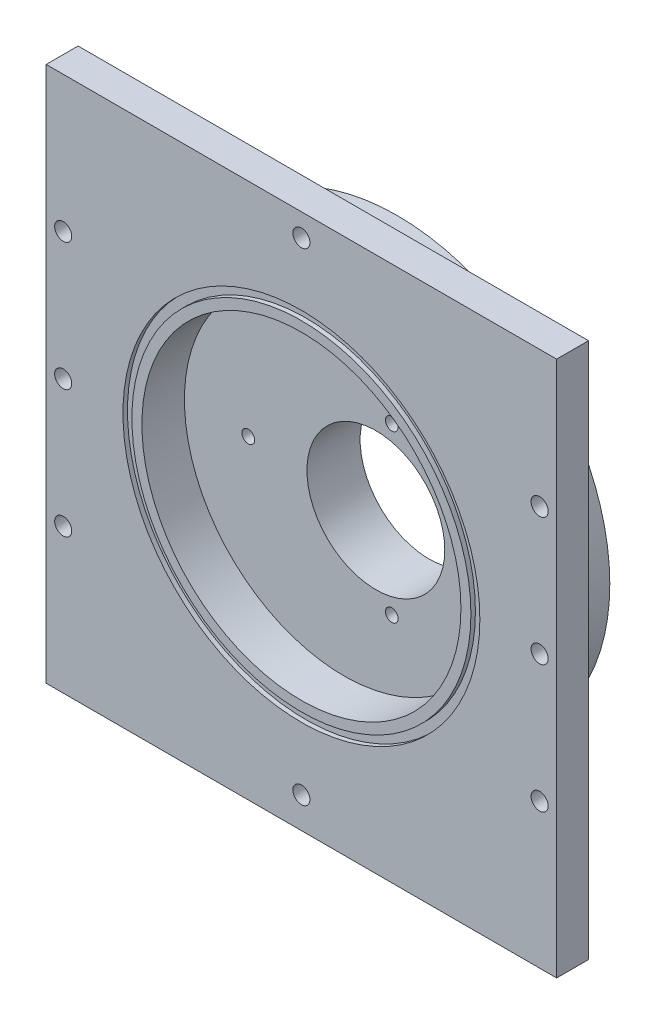
SolidWorks part; units mm, degrees
ref_plane "Front Plane" through (0, 0, 0) normal (0, 0, 1) x (1, 0, 0)
ref_plane "Top Plane" through (0, 0, 0) normal (0, 1, 0) x (1, 0, 0)
ref_plane "Right Plane" through (0, 0, 0) normal (1, 0, 0) x (0, 0, -1)
ref_plane "Plane1" through (0, 0, 0) normal (0, 0, -1) x (-1, 0, 0)
sketch "Sketch1" plane through (0, 0, 0) normal (0, 0, -1) x (-1, 0, 0)
  line L0 (76.2, 76.2) -> (-76.2, 76.2)
  line L1 (-76.2, 76.2) -> (-76.2, -81.28)
  line L2 (-76.2, -81.28) -> (76.2, -81.28)
  line L3 (76.2, -81.28) -> (76.2, 76.2)
  dimension "D1" = 157.48
  dimension "D2" = 152.4
extrude "Boss-Extrude1" add sketch "Sketch1" against normal blind 9.525
sketch "Sketch16" plane through (0, 76.2, 0) normal (0, 1, 0) x (1, 0, 0)
  line L1 (-76.2, -9.525) -> (76.2, -9.525)
  line L2 (-76.2, -9.525) -> (-76.2, 0)
  line L3 (-76.2, 0) -> (76.2, 0)
  line L4 (76.2, -9.525) -> (76.2, 0)
extrude "Boss-Extrude2" add sketch "Sketch16" along normal blind 2.54
hole_wizard "M100 Clearance Hole1" positions "Sketch3" profile "Sketch2" hole size "M100" standard "ANSI Metric"
sketch "Sketch3" plane through (0, 0, 9.525) normal (0, 0, 1) x (1, 0, 0)
  point P0 (0, 0)
sketch "Sketch2" plane through (0, 0, 9.525) normal (1, 0, 0) x (0, -1, 0)
  line L0 (0, 0) -> (0, 1.3462)
  line L1 (0, 1.3462) -> (53.2765, 1.3462)
  line L2 (53.2765, 1.3462) -> (53.2765, 0)
  line L5 (53.2765, 0) -> (0, 0)
  line L10 (0, 1.3462) -> (-53.2765, 1.3462) construction
  line L11 (0, -6.35) -> (0, 107.95) construction
  dimension "Hole Dia." = 106.553
  dimension "Hole Depth" = 1.3462
  dimension "Drill Angle" = 180
sketch "Sketch4" plane through (0, 0, 0) normal (0, 1, 0) x (1, 0, 0)
  line L0 (63.5, 19.05) -> (0, 19.05)
  line L1 (0, 19.05) -> (0, 0)
  line L2 (0, 0) -> (63.5, 0)
  line L3 (63.5, 0) -> (63.5, 19.05)
  line L4 (0, 19.05) -> (0, 0) construction
revolve "Revolve1" add sketch "Sketch4" angle 360 about L4
sketch "Sketch5" plane through (0, 0, 0) normal (0, 1, 0) x (1, 0, 0)
  line L0 (50.6095, -8.1788) -> (0, -8.1788)
  line L1 (0, -8.1788) -> (0, -9.525)
  line L2 (0, -9.525) -> (50.6095, -9.525)
  line L3 (50.6095, -9.525) -> (50.6095, -8.1788)
  line L4 (0, -8.1788) -> (0, -9.525) construction
revolve "Revolve2" add sketch "Sketch5" angle 360 about L4
hole_wizard "CBORE for #10 Socket Head Cap Screw1" positions "Sketch7" profile "Sketch6" counterbore size "#10" standard "ANSI Inch" end condition through all
sketch "Sketch7" plane through (0, 0, 0) normal (0, 0, -1) x (-1, 0, 0)
  line L0 (-76.2, -81.28) -> (76.2, -81.28) construction
  line L2 (-76.2, 78.74) -> (-76.2, -81.28) construction
  line L3 (76.2, 76.2) -> (-76.2, 76.2) construction
  point P0 (71.12, 38.1)
  point P1 (71.12, -38.1)
  point P2 (-71.12, 38.1)
  point P3 (-71.12, -38.1)
  point P4 (0, 72.009)
  point P5 (0, -72.009)
  point P6 (71.12, 0)
  point P7 (-71.12, 0)
  point P9 (0, -81.28)
  dimension "D1" = 144.018
  dimension "D2" = 9.271
  dimension "D3" = 76.2
  dimension "D4" = 76.2
  dimension "D5" = 4.191
sketch "Sketch6" plane through (-71.12, 38.1, 0) normal (1, 0, 0) x (0, 1, 0)
  line L0 (0, 0) -> (0, 9.525)
  line L1 (0, 9.525) -> (2.5527, 9.525)
  line L3 (2.5527, 9.525) -> (2.5527, 4.826)
  line L4 (2.5527, 4.826) -> (4.7625, 4.826)
  line L5 (4.7625, 4.826) -> (4.7625, 0)
  line L7 (4.7625, 0) -> (0, 0)
  line L11 (0, -6.35) -> (0, 107.95) construction
  dimension "Thru Hole Dia." = 5.1054
  dimension "Thru Hole Depth" = 9.525
  dimension "C'Bore Dia." = 9.525
  dimension "C'Bore Depth" = 4.826
hole_wizard "#10-24 Tapped Hole1" positions "Sketch9" profile "Sketch8" tap size "#10-24" standard "ANSI Inch"
sketch "Sketch9" plane through (0, 0, -19.05) normal (0, 0, -1) x (-1, 0, 0)
  point P0 (17.3114, 15.494)
  point P1 (17.3114, -15.494)
  point P2 (-9.525, -30.988)
  point P3 (-36.3614, -15.494)
  point P4 (-36.3614, 15.494)
  point P5 (-9.525, 30.988)
sketch "Sketch8" plane through (-17.3114, 15.494, -19.05) normal (1, 0, 0) x (0, 1, 0)
  line L0 (0, 0) -> (0, 10.0308)
  line L1 (0, 10.0308) -> (1.8986, 8.89)
  line L2 (1.8986, 8.89) -> (1.8986, 0)
  line L5 (1.8986, 0) -> (0, 0)
  line L10 (0, 10.0308) -> (-1.8987, 8.89) construction
  line L11 (0, -6.35) -> (0, 107.95) construction
  dimension "Tap Drill Dia." = 3.7973
  dimension "Tap Drill Depth" = 8.89
  dimension "Drill Angle" = 118
hole_wizard "M90 Clearance Hole1" positions "Sketch11" profile "Sketch10" hole size "M90" standard "ANSI Metric"
sketch "Sketch11" plane through (0, 0, 9.525) normal (0, 0, 1) x (1, 0, 0)
  point P0 (0, 0)
sketch "Sketch10" plane through (0, 0, 9.525) normal (1, 0, 0) x (0, -1, 0)
  line L0 (0, 0) -> (0, 12.7)
  line L1 (0, 12.7) -> (47.625, 12.7)
  line L2 (47.625, 12.7) -> (47.625, 0)
  line L5 (47.625, 0) -> (0, 0)
  line L10 (0, 12.7) -> (-47.625, 12.7) construction
  line L11 (0, -6.35) -> (0, 107.95) construction
  dimension "Hole Dia." = 95.25
  dimension "Hole Depth" = 12.7
  dimension "Drill Angle" = 180
hole_wizard "M36 Clearance Hole1" positions "Sketch13" profile "Sketch12" hole size "M36" standard "ANSI Metric"
sketch "Sketch13" plane through (0, 0, -3.175) normal (0, 0, 1) x (1, 0, 0)
  point P0 (9.525, 0)
sketch "Sketch12" plane through (9.525, 0, -3.175) normal (1, 0, 0) x (0, -1, 0)
  line L0 (0, 0) -> (0, 15.875)
  line L1 (0, 15.875) -> (20.574, 15.875)
  line L2 (20.574, 15.875) -> (20.574, 0)
  line L5 (20.574, 0) -> (0, 0)
  line L11 (0, -6.35) -> (0, 107.95) construction
  dimension "Thru Hole Dia." = 41.148
  dimension "Thru Hole Depth" = 15.875
hole_wizard "#10-24 Tapped Hole2" positions "Sketch15" profile "Sketch14" tap size "#10-24" standard "ANSI Inch"
sketch "Sketch15" plane through (0, 0, -3.175) normal (0, 0, 1) x (1, 0, 0)
  point P0 (14.2875, -24.7467)
  point P1 (-28.575, 0)
  point P2 (14.2875, 24.7467)
sketch "Sketch14" plane through (14.2875, -24.7467, -3.175) normal (1, 0, 0) x (0, -1, 0)
  line L0 (0, 0) -> (0, 8.8904)
  line L1 (0, 8.8904) -> (1.8986, 7.7495)
  line L2 (1.8986, 7.7495) -> (1.8986, 0)
  line L5 (1.8986, 0) -> (0, 0)
  line L10 (0, 8.8904) -> (-1.8987, 7.7495) construction
  line L11 (0, -6.35) -> (0, 107.95) construction
  dimension "Tap Drill Dia." = 3.7973
  dimension "Tap Drill Depth" = 7.7495
  dimension "Drill Angle" = 118
